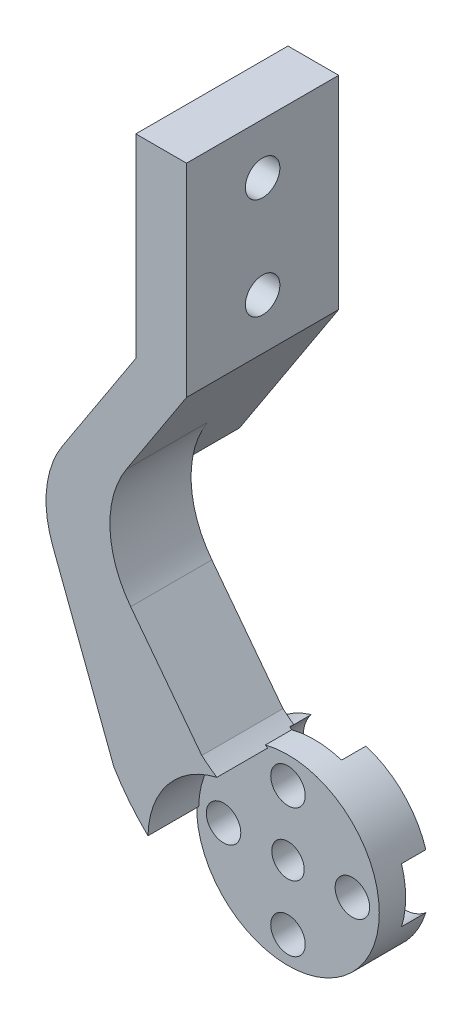
SolidWorks part; units mm, degrees
ref_plane "정면" through (0, 0, 0) normal (0, 0, 1) x (1, 0, 0)
ref_plane "윗면" through (0, 0, 0) normal (0, 1, 0) x (1, 0, 0)
ref_plane "우측면" through (0, 0, 0) normal (1, 0, 0) x (0, 0, -1)
sketch "스케치1" plane through (0, 0, 0) normal (0, 0, 1) x (1, 0, 0)
  line L0 (0, 0) -> (0, 11.2508) construction
  line L1 (0, 0) -> (1.9881, 6.7117) construction
  line L2 (0, 0) -> (-6.1517, -3.3401) construction
  line L3 (-3.4934, 9.6879) -> (6.2483, 21.094) construction
  line L4 (6.2483, 21.094) -> (1.9881, 6.7117) construction
  line L5 (-8.9141, 0.2926) -> (4.9791, 14.6794) construction
  line L6 (4.9791, 14.6794) -> (-12.1643, 4.3786) construction
  line L7 (-8.9141, 0.2926) -> (-19.334, -10.4975) construction
  line L8 (-19.334, -10.4975) -> (-6.1517, -3.3401) construction
  line L9 (-12.1643, 4.3786) -> (-20, 25)
  line L10 (-20, 25) -> (-10, 40.3333)
  line L12 (-5, 39.5) -> (-14.7826, 24.5)
  line L13 (-14.7826, 24.5) -> (-3.4934, 9.6879)
  line L17 (-5, 39.5) -> (-5, 59.5)
  line L18 (-5, 59.5) -> (-10, 59.5)
  line L19 (-10, 40.3333) -> (-10, 59.5)
  arc A0 (1.9881, 6.7117) -> (-6.1517, -3.3401) centre (0, 0) cw
  circle A1 centre (0, 0) radius 1.6
  arc A2 (1.9881, 6.7117) -> (-3.4934, 9.6879) centre (6.2483, 21.094) cw
  arc A3 (-6.1517, -3.3401) -> (-8.9141, 0.2926) centre (-19.334, -10.4975) ccw
  arc A4 (-8.9141, 0.2926) -> (-12.1643, 4.3786) centre (4.9791, 14.6794) cw
  dimension "D1" = 7
  dimension "D2" = 3.2
  dimension "D3" = 15
  dimension "D6" = 20
  dimension "D4" = 16.5
  dimension "D5" = 225
  dimension "D7" = 24
  dimension "D8" = 17.5
  dimension "D9" = 15
  dimension "D10" = 15
  dimension "D11" = 35
  dimension "D12" = 25
  dimension "D13" = 24.5
  dimension "D15" = 5.2174
  dimension "D16" = 20
  dimension "D17" = 5
  dimension "D18" = 20
  dimension "D19" = 4.6433
extrude "보스-돌출1" add sketch "스케치1" along normal blind 8
sketch "스케치2" plane through (0, 0, 8) normal (0, 0, 1) x (1, 0, 0)
  line L5 (-14.7826, 24.5) -> (-18.6719, 27.0365)
  line L6 (-10, 40.3333) -> (-20, 25) construction
  line L7 (-18.6719, 27.0365) -> (-10, 40.3333)
  line L8 (-10, 40.3333) -> (-10, 59.5)
  line L9 (-10, 59.5) -> (-10, 40.3333) construction
  line L10 (-10, 59.5) -> (-5, 59.5)
  line L11 (-5, 59.5) -> (-5, 39.5)
  line L12 (-5, 39.5) -> (-14.7826, 24.5)
extrude "보스-돌출2" add sketch "스케치2" against normal blind 15
fillet "필렛1" radius 10 2 edges at (-14.7826, 24.5, 4) (-20, 25, 4)
sketch "스케치3" plane through (0, 0, 8) normal (0, 0, 1) x (1, 0, 0)
  circle A0 centre (0, 0) radius 8.8
  dimension "D1" = 17.6
extrude "컷-돌출1" cut sketch "스케치3" against normal blind 5
sketch "스케치4" plane through (0, 0, 0) normal (0, 0, -1) x (-1, 0, 0)
  circle A0 centre (0, 0) radius 9
  circle A1 centre (0, 0) radius 1.6
  dimension "D1" = 18
extrude "보스-돌출3" add sketch "스케치4" along normal blind 2 and the other way up to surface other way up to face at (1.6, 0, 3)
hole_wizard "M3 남비 머리 나사용 카운터보어1" positions "스케치5" profile "스케치6" counterbore size "M3" standard "ISO" end condition through all
sketch "스케치5" plane through (0, 0, -2) normal (0, 0, -1) x (-1, 0, 0)
  point P0 (0, 6.35)
  point P8 (6.35, 0)
  point P9 (0, -6.35)
  point P10 (-6.35, 0)
  dimension "D1" = 6.35
  dimension "D2" = 4
sketch "스케치6" plane through (0, 6.35, -2) normal (1, 0, 0) x (0, 1, 0)
  line L0 (0, 0) -> (0, 10)
  line L1 (0, 10) -> (1.7, 10)
  line L3 (1.7, 10) -> (1.7, 2.4)
  line L4 (1.7, 2.4) -> (3.5, 2.4)
  line L5 (3.5, 2.4) -> (3.5, 0)
  line L7 (3.5, 0) -> (0, 0)
  line L11 (0, -6.35) -> (0, 107.95) construction
  dimension "관통 구멍 지름" = 3.4
  dimension "관통 구멍 깊이" = 10
  dimension "카운터보어 지름" = 7
  dimension "카운터보어 깊이" = 2.4
hole_wizard "M3 여유 구멍1" positions "스케치7" profile "스케치8" hole size "M3" standard "ISO" end condition through all
sketch "스케치7" plane through (-10, 0, 0) normal (-1, 0, 0) x (0, 0, 1)
  line L0 (-7, 59.5) -> (8, 59.5) construction
  point P0 (0.5, 54.5)
  point P2 (0.5, 44.5)
  point P7 (0.5, 59.5)
  dimension "D1" = 5
  dimension "D2" = 10
sketch "스케치8" plane through (-10, 54.5, 0.5) normal (0, 1, 0) x (0, 0, 1)
  line L0 (0, 0) -> (0, 19)
  line L1 (0, 19) -> (1.7, 19)
  line L2 (1.7, 19) -> (1.7, 0)
  line L5 (1.7, 0) -> (0, 0)
  line L11 (0, -6.35) -> (0, 107.95) construction
  dimension "관통 구멍 지름" = 3.4
  dimension "관통 구멍 깊이" = 19
